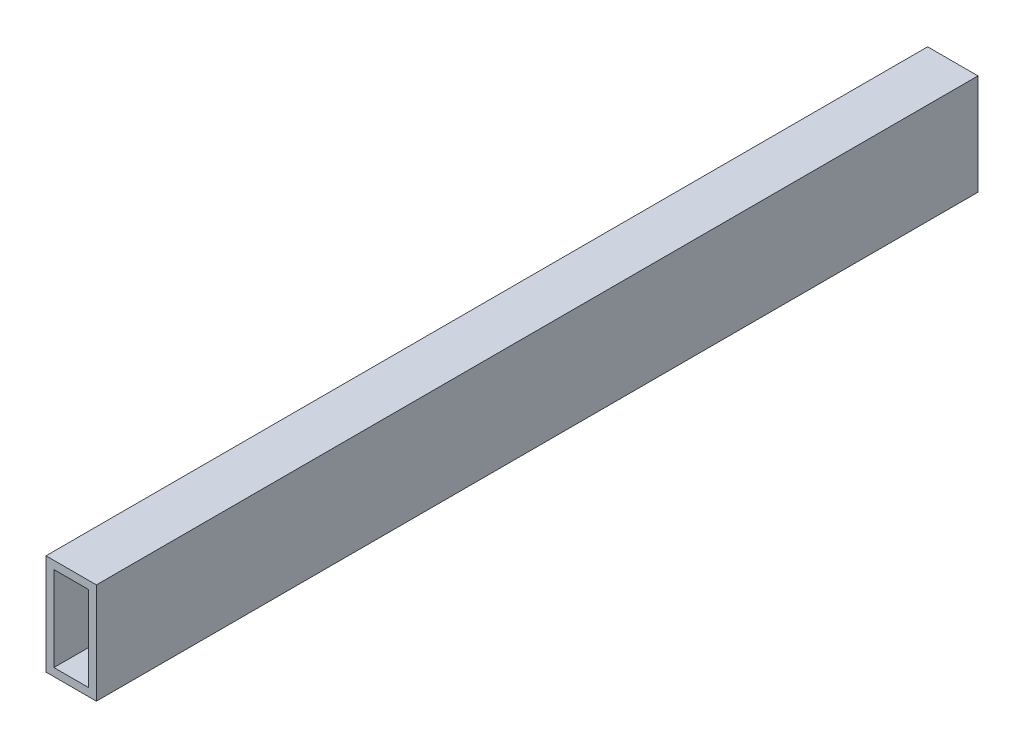
SolidWorks part; units mm, degrees
material "1.0045 (S355JR)"
ref_plane "Front Plane" through (0, 0, 0) normal (0, 0, 1) x (1, 0, 0)
ref_plane "Top Plane" through (0, 0, 0) normal (0, 1, 0) x (1, 0, 0)
ref_plane "Right Plane" through (0, 0, 0) normal (1, 0, 0) x (0, 0, -1)
curve "Curve1"
  spline degree 1 poles (0, 0, -350) (0, 0, 350) knots 0 0 1 1
sketch "Sketch1" plane through (0, 0, 0) normal (0, 0, 1) x (1, 0, 0)
  line L0 (0, 35.3535) -> (0, -33.8384) construction
  line L1 (-20, 40) -> (20, 40)
  line L2 (-20, 40) -> (-20, -40)
  line L3 (-20, -40) -> (20, -40)
  line L4 (20, 40) -> (20, -40)
  line L5 (-13.7, 33.7) -> (13.7, 33.7)
  line L6 (-13.7, 33.7) -> (-13.7, -33.7)
  line L7 (-13.7, -33.7) -> (13.7, -33.7)
  line L8 (13.7, 33.7) -> (13.7, -33.7)
  line L9 (-39.3939, 0) -> (41.5152, 0) construction
  dimension "D1" = 40
  dimension "D2" = 27.4
  dimension "D3" = 80
  dimension "D4" = 67.4
sweep "Sweep1" add profiles "Sketch1" path "Curve1"
